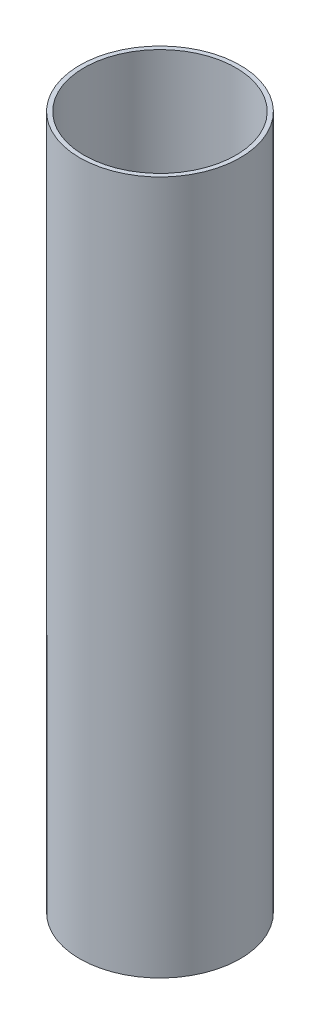
SolidWorks part; units mm, degrees
material "Epoxy, Unfilled"
ref_plane "Front Plane" through (0, 0, 0) normal (0, 0, 1) x (1, 0, 0)
ref_plane "Top Plane" through (0, 0, 0) normal (0, 1, 0) x (1, 0, 0)
ref_plane "Right Plane" through (0, 0, 0) normal (1, 0, 0) x (0, 0, -1)
sketch "Sketch2" plane through (0, 0, 0) normal (0, 1, 0) x (1, 0, 0)
  circle A0 centre (0, 0) radius 58.7375
  circle A1 centre (0, 0) radius 55.5625
extrude "Boss-Extrude1" add sketch "Sketch2" along normal blind 508
